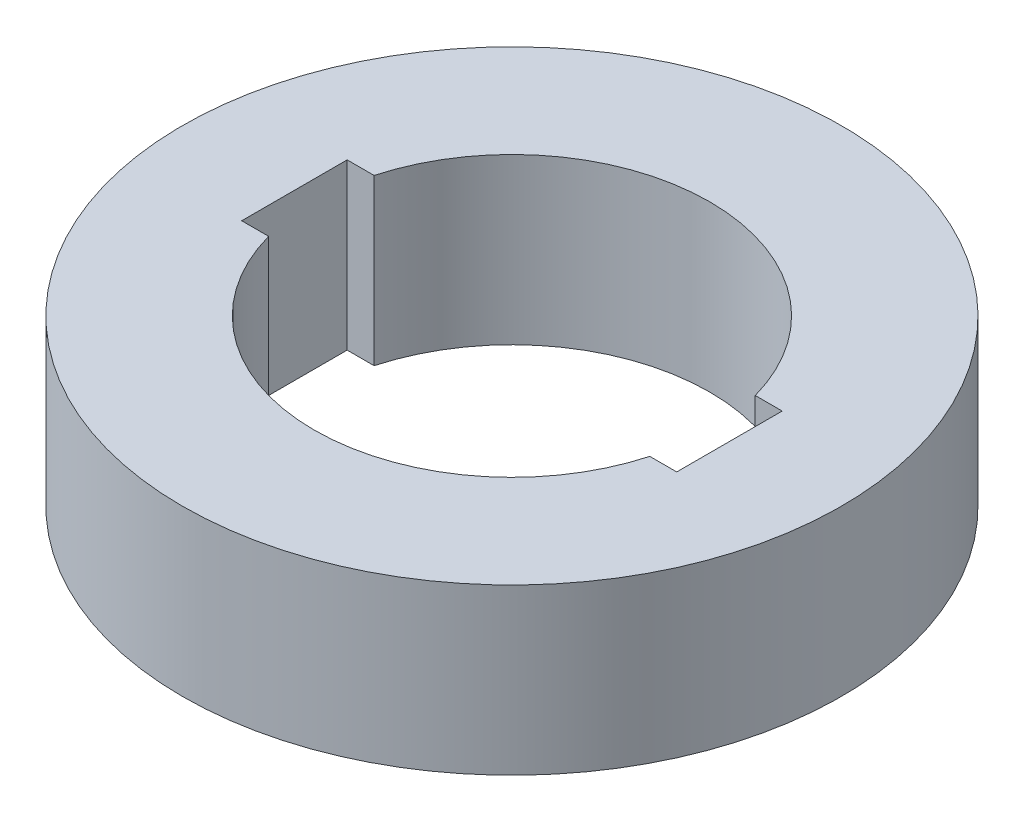
SolidWorks part; units mm, degrees
ref_plane "Front Plane" through (0, 0, 0) normal (0, 0, 1) x (1, 0, 0)
ref_plane "Top Plane" through (0, 0, 0) normal (0, 1, 0) x (1, 0, 0)
ref_plane "Right Plane" through (0, 0, 0) normal (1, 0, 0) x (0, 0, -1)
sketch "Sketch2" plane through (0, 0, 0) normal (0, 1, 0) x (1, 0, 0)
  line L0 (28.9137, 8) -> (33, 8)
  line L1 (-33, 8) -> (-28.9137, 8)
  line L2 (-33, 8) -> (-33, -8)
  line L3 (-33, -8) -> (-28.9137, -8)
  line L4 (33, 8) -> (33, -8)
  line L5 (28.9137, -8) -> (33, -8)
  circle A0 centre (0, 0) radius 50
  arc A1 (-28.9137, -8) -> (28.9137, -8) centre (0, 0) ccw
  arc A2 (28.9137, 8) -> (-28.9137, 8) centre (0, 0) ccw
  dimension "D1" = 100
  dimension "D2" = 60
  dimension "D3" = 8
  dimension "D4" = 33
  dimension "D5" = 16
  dimension "D6" = 66
extrude "Boss-Extrude1" add sketch "Sketch2" along normal blind 25
